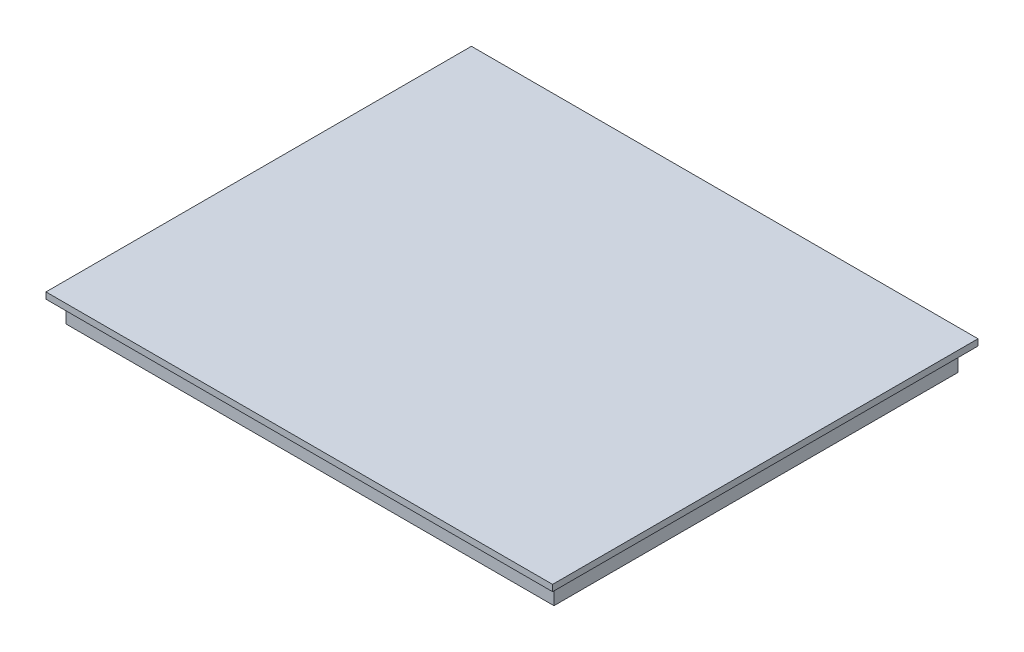
SolidWorks part; units mm, degrees
ref_plane "前视基准面" through (0, 0, 0) normal (0, 0, 1) x (1, 0, 0)
ref_plane "上视基准面" through (0, 0, 0) normal (0, 1, 0) x (1, 0, 0)
ref_plane "右视基准面" through (0, 0, 0) normal (1, 0, 0) x (0, 0, -1)
sketch "草图1" plane through (0, 0, 0) normal (0, 1, 0) x (1, 0, 0)
  line L1 (-38.35, 31.75) -> (38.35, 31.75)
  line L2 (-38.35, 31.75) -> (-38.35, -31.75)
  line L3 (-38.35, -31.75) -> (38.35, -31.75)
  line L4 (38.35, 31.75) -> (38.35, -31.75)
  line L5 (-38.35, 31.75) -> (38.35, -31.75) construction
  line L6 (-38.35, -31.75) -> (38.35, 31.75) construction
  point P0 (0, 0)
  dimension "D1" = 63.5
  dimension "D2" = 76.7
extrude "凸台-拉伸1" add sketch "草图1" along normal blind 3.5
sketch "草图2" plane through (0, 3.5, 0) normal (0, 1, 0) x (1, 0, 0)
  line L1 (-39.83, 33.45) -> (39.83, 33.45)
  line L2 (-39.83, 33.45) -> (-39.83, -33.45)
  line L3 (-39.83, -33.45) -> (39.83, -33.45)
  line L4 (39.83, 33.45) -> (39.83, -33.45)
  line L5 (-39.83, 33.45) -> (39.83, -33.45) construction
  line L6 (-39.83, -33.45) -> (39.83, 33.45) construction
  point P0 (0, 0)
  dimension "D1" = 66.9
  dimension "D2" = 79.66
extrude "凸台-拉伸2" add sketch "草图2" along normal blind 1
